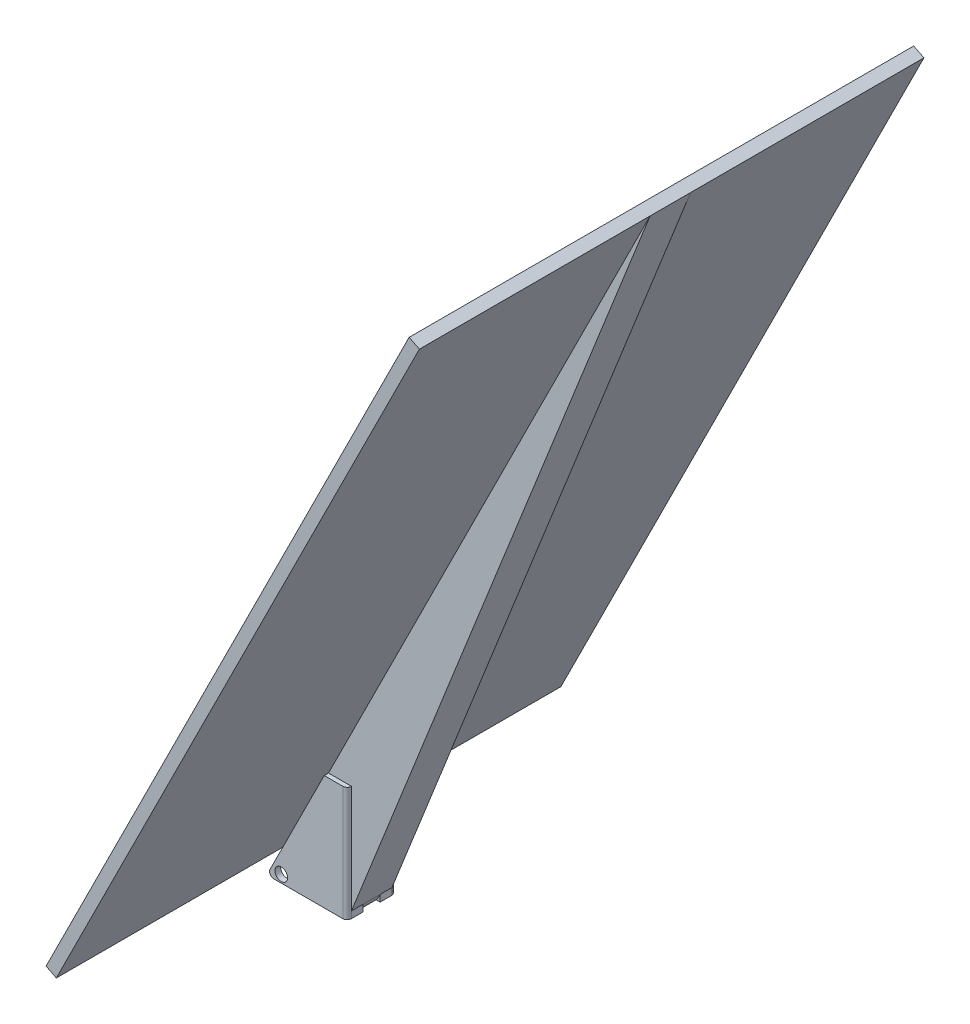
SolidWorks part; units mm, degrees
ref_plane "Front Plane" through (0, 0, 0) normal (0, 0, 1) x (1, 0, 0)
ref_plane "Top Plane" through (0, 0, 0) normal (0, 1, 0) x (1, 0, 0)
ref_plane "Right Plane" through (0, 0, 0) normal (1, 0, 0) x (0, 0, -1)
sketch "Sketch1" plane through (0, 0, 0) normal (0, 0, 1) x (1, 0, 0)
  line L0 (-3.175, 19.685) -> (-34.925, -43.815)
  line L1 (9.525, -43.815) -> (-34.925, -43.815)
  line L2 (9.525, -43.815) -> (9.525, 19.685)
  line L3 (9.525, 19.685) -> (-3.175, 19.685)
  point P0 (0, 0)
  dimension "D1" = 44.45
  dimension "D2" = 12.7
  dimension "2.5" = 63.5
extrude "Boss-Extrude1" add sketch "Sketch1" along normal blind 26.9875
sketch "Sketch2" plane through (0, 19.685, 0) normal (0, 1, 0) x (1, 0, 0)
  line L0 (-34.925, -3.175) -> (6.35, -3.175)
  line L1 (-34.925, -26.9875) -> (-34.925, 0) construction
  line L2 (6.35, -3.175) -> (6.35, -23.8125)
  line L3 (6.35, -23.8125) -> (-34.925, -23.8125)
  line L4 (-34.925, -23.8125) -> (-34.925, -3.175)
  line L5 (-3.175, 0) -> (-34.925, 0) construction
  line L6 (-3.175, -26.9875) -> (-34.925, -26.9875) construction
  line L7 (9.525, -26.9875) -> (9.525, 0) construction
  dimension "D1" = 3.175
  dimension "D2" = 3.175
  dimension "D3" = 3.175
extrude "Cut-Extrude1" cut sketch "Sketch2" against normal through all
sketch "Sketch3" plane through (0, 0, 26.9875) normal (0, 0, 1) x (1, 0, 0)
  circle A0 centre (-26.9655, -39.5437) radius 3.4988
  dimension "D1" = 6.9977
extrude "Cut-Extrude2" cut sketch "Sketch3" against normal through all
fillet "Fillet1" radius 2.38 2 edges at (9.525, -12.065, 26.9875) (9.525, -12.065, 0)
fillet "Fillet2" radius 2.38 2 edges at (-34.925, -43.815, 1.5875) (-34.925, -43.815, 25.4)
sketch "Sketch5" plane through (9.525, 0, 0) normal (1, 0, 0) x (0, 0, -1)
  line L0 (-24.6075, 19.685) -> (-2.38, 19.685) construction
  circle A0 centre (-12.4886, 8.5725) radius 3.9688
  dimension "D2" = 7.9375
  dimension "D1" = 11.1125
extrude "Cut-Extrude3" cut sketch "Sketch5" against normal through all
sketch "Sketch6" plane through (9.525, 0, 0) normal (1, 0, 0) x (0, 0, -1)
  line L0 (-8.7312, -43.815) -> (-18.2562, -43.815)
  line L1 (-24.6075, -43.815) -> (-2.38, -43.815) construction
  line L2 (-13.4938, 26.2675) -> (-13.4937, -60.0038) construction
  line L3 (-18.2562, -43.815) -> (-18.2563, -32.7025)
  line L4 (-8.7312, -43.815) -> (-8.7312, -32.7025)
  arc A0 (-18.2563, -32.7025) -> (-8.7312, -32.7025) centre (-13.4938, -32.7025) cw
  point P7 (-13.4937, -43.815)
  dimension "D1" = 4.7625
  dimension "D2" = 11.1125
extrude "Cut-Extrude4" cut sketch "Sketch6" against normal through all
ref_plane "Plane1" through (-10.414, 5.207, 0) normal (-0.8944, 0.4472, 0) x (0, 0, 1)
sketch "Sketch7" plane through (-10.414, 5.207, 0) normal (-0.8944, 0.4472, 0) x (0, 0, 1)
  line L0 (0, -50.9573) -> (26.9875, -50.9573) construction
  line L3 (-127, -35.0823) -> (152.4, -35.0823)
  line L4 (-127, -35.0823) -> (-127, 414.4977)
  line L5 (-127, 414.4977) -> (152.4, 414.4977)
  line L6 (152.4, -35.0823) -> (152.4, 414.4977)
  dimension "D1" = 449.58
  dimension "D2" = 279.4
  dimension "D3" = 15.875
extrude "Boss-Extrude2" add sketch "Sketch7" along normal blind 6.35
sketch "Sketch11" plane through (-10.414, 5.207, 0) normal (0.8944, -0.4472, 0) x (0, 0, -1)
  line L0 (-152.4, 414.4977) -> (127, 414.4977) construction
  line L1 (-24.6075, -34.9296) -> (-2.2032, -34.9296)
  line L2 (-24.6075, -34.9296) -> (-24.6075, 414.4977)
  line L3 (-24.6075, 414.4977) -> (-2.2032, 414.4977)
  line L4 (-2.2032, -34.9296) -> (-2.2032, 414.4977)
extrude "Boss-Extrude3" add sketch "Sketch11" along normal blind 38.1
sketch "Sketch12" plane through (0, 0, 2.2032) normal (0, 0, -1) x (-1, 0, 0)
  line L0 (-9.5184, -40.1223) -> (-9.5184, 19.685)
  line L1 (-9.5184, 19.685) -> (-191.9938, 367.4256)
  line L2 (-209.0327, 358.9061) -> (-174.955, 375.945) construction
  line L3 (-191.9938, 367.4256) -> (-209.0327, 358.9061)
  line L4 (-209.0327, 358.9061) -> (-9.5184, -40.1223)
sketch "Sketch13" plane through (0, 0, 24.6075) normal (0, 0, 1) x (1, 0, 0)
  line L0 (174.955, 375.945) -> (9.525, -40.1092)
  line L1 (9.525, -40.1092) -> (209.0327, 358.9061)
  line L2 (209.0327, 358.9061) -> (174.955, 375.945)
extrude "Cut-Extrude6" cut sketch "Sketch13" against normal through all
